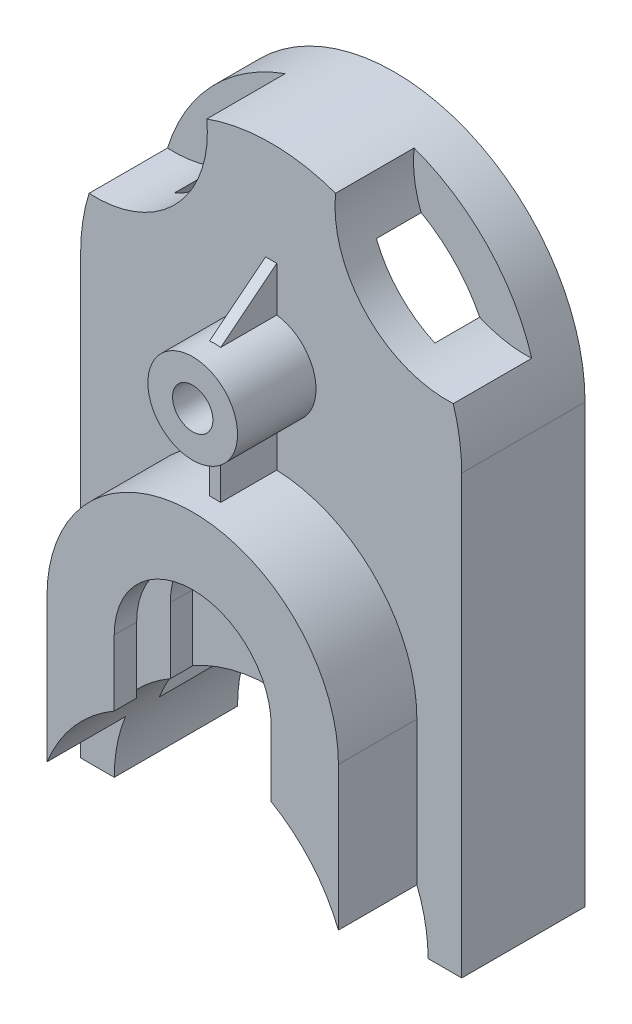
SolidWorks part; units mm, degrees
ref_plane "Front Plane" through (0, 0, 0) normal (0, 0, 1) x (1, 0, 0)
ref_plane "Top Plane" through (0, 0, 0) normal (0, 1, 0) x (1, 0, 0)
ref_plane "Right Plane" through (0, 0, 0) normal (1, 0, 0) x (0, 0, -1)
sketch "Sketch1" plane through (0, 0, 0) normal (0, 0, 1) x (1, 0, 0)
  line L1 (0, 0) -> (170, 0)
  line L2 (0, 0) -> (0, 280)
  line L3 (0, 280) -> (170, 280)
  line L4 (170, 0) -> (170, 280)
  dimension "D1" = 170
  dimension "D2" = 280
extrude "Boss-Extrude1" add sketch "Sketch1" along normal blind 90
sketch "Sketch2" plane through (0, 0, 90) normal (0, 0, 1) x (1, 0, 0)
  line L0 (170, 0) -> (170, 280) construction
  line L1 (0, 195) -> (0, 280)
  line L2 (0, 280) -> (170, 280)
  line L3 (170, 280) -> (170, 195)
  arc A0 (170, 195) -> (0, 195) centre (85, 195) ccw
  line M1 (0, 280) -> (0, 0)
  line M3 (170, 0) -> (170, 280)
  line M4 (170, 280) -> (0, 280)
  dimension "D1" = 85
  dimension "D2" = 85
  dimension "D3" = 85
  dimension "D4" = 85
  dimension "D5" = 195
  dimension "D6" = 170
  dimension "D7" = 85
  dimension "D8" = 280
  dimension "D9" = 170
  dimension "D10" = 85
extrude "Cut-Extrude1" cut sketch "Sketch2" against normal blind 90 contours A0 L2 M1 | A0 M3 M4
sketch "Sketch3" plane through (0, 0, 90) normal (0, 0, 1) x (1, 0, 0)
  line L0 (0, 0) -> (170, 0) construction
  line L1 (15, 0) -> (155, 0)
  arc A0 (155, 0) -> (15, 0) centre (85, 0) ccw
  dimension "D1" = 15
  dimension "D2" = 15
extrude "Cut-Extrude2" cut sketch "Sketch3" against normal blind 90
sketch "Sketch4" plane through (0, 0, 0) normal (0, 1, 0) x (1, 0, 0)
  line L1 (0, -90) -> (20, -90)
  line L2 (0, -90) -> (0, -55)
  line L3 (0, -55) -> (20, -55)
  line L4 (20, -90) -> (20, -55)
  line L5 (170, -90) -> (150, -90)
  line L6 (170, -90) -> (170, -55)
  line L7 (170, -55) -> (150, -55)
  line L8 (150, -90) -> (150, -55)
  dimension "D1" = 20
  dimension "D2" = 20
  dimension "D3" = 35
  dimension "D4" = 35
extrude "Cut-Extrude3" cut sketch "Sketch4" along normal blind 299
sketch "Sketch5" plane through (0, 0, 0) normal (0, 0, -1) x (-1, 0, 0)
  line L0 (-20, 195) -> (-20, 25.9808)
  line L1 (-150, 195) -> (-150, 25.9808)
  arc A0 (-20, 195) -> (-150, 195) centre (-85, 195) ccw
  arc A1 (-15, 0) -> (-155, 0) centre (-85, 0) ccw construction
  arc A2 (-20, 25.9808) -> (-150, 25.9808) centre (-85, 0) ccw
  arc M2 (-155, 0) -> (-15, 0) centre (-85, 0) cw
  dimension "D3" = 65
  dimension "D1" = 20
  dimension "D2" = 20
extrude "Cut-Extrude4" cut sketch "Sketch5" against normal blind 40 contours L0 A0 L1 M2
sketch "Sketch6" plane through (0, 0, 90) normal (0, 0, 1) x (1, 0, 0)
  circle A0 centre (85, 90) radius 9
  arc A1 (150, 249.7723) -> (20, 249.7723) centre (85, 195) ccw construction
  dimension "D1" = 18
  dimension "D2" = 85
  dimension "D3" = 90
extrude "Cut-Extrude5" cut sketch "Sketch6" against normal blind 50
sketch "Sketch7" plane through (0, 0, 90) normal (0, 0, 1) x (1, 0, 0)
  line L0 (150, 249.7723) -> (150, 25.9808) construction
  line L1 (20, 90) -> (20, 249.7723)
  line L2 (150, 90) -> (150, 249.7723)
  arc A0 (150, 90) -> (20, 90) centre (85, 90) ccw
  arc A1 (150, 249.7723) -> (20, 249.7723) centre (85, 195) ccw
  dimension "D1" = 90
  dimension "D2" = 90
  dimension "D3" = 130
  dimension "D4" = 249.7723
extrude "Cut-Extrude6" cut sketch "Sketch7" against normal blind 35
sketch "Sketch8" plane through (0, 0, 90) normal (0, 0, 1) x (1, 0, 0)
  line L0 (50, 90) -> (50, 60.6218)
  line L1 (120, 90) -> (120, 60.6218)
  arc A0 (120, 90) -> (50, 90) centre (85, 90) ccw
  arc A3 (150, 25.9808) -> (20, 25.9808) centre (85, 0) ccw construction
  arc A4 (50, 60.6218) -> (120, 60.6218) centre (85, 0) cw
  circle M1 centre (85, 90) radius 9
  arc M5 (20, 25.9808) -> (150, 25.9808) centre (85, 0) cw
  dimension "D1" = 35
  dimension "D2" = 90
  dimension "D3" = 90
extrude "Cut-Extrude7" cut sketch "Sketch8" against normal blind 35 contours L1 A0 L0 M5 M1
ref_plane "Plane1" through (0, 0, 80) normal (0, 0, 1) x (1, 0, 0)
sketch "Sketch9" plane through (0, 0, 80) normal (0, 0, 1) x (1, 0, 0)
  line L0 (35, 90) -> (50, 90)
  line L1 (120, 90) -> (135, 90)
  line L2 (35, 90) -> (35, 48.9898)
  line L3 (135, 90) -> (135, 48.9898)
  arc A0 (135, 90) -> (35, 90) centre (85, 90) ccw
  arc A1 (50, 90) -> (120, 90) centre (85, 90) cw
  arc A2 (15, 0) -> (155, 0) centre (85, 0) cw
  dimension "D1" = 50
  dimension "D2" = 90
  dimension "D3" = 90
  dimension "D4" = 15
  dimension "D5" = 15
extrude "Cut-Extrude9" cut sketch "Sketch9" against normal blind 15 contours L0 A1 L1 A0 | L2 A2 L3 L1 A1 L0
sketch "Sketch10" plane through (0, 0, 55) normal (0, 0, 1) x (1, 0, 0)
  circle A0 centre (85, 195) radius 20
  dimension "D1" = 40
extrude "Boss-Extrude2" add sketch "Sketch10" along normal blind 35
sketch "Sketch11" plane through (0, 0, 90) normal (0, 0, 1) x (1, 0, 0)
  circle A0 centre (85, 195) radius 9
  dimension "D1" = 18
extrude "Cut-Extrude10" cut sketch "Sketch11" against normal blind 35
sketch "Sketch12" plane through (0, 0, 55) normal (0, 0, 1) x (1, 0, 0)
  line L0 (0, 195) -> (0, 0) construction
  line L1 (82.5, 214.8431) -> (87.5, 214.8431)
  line L2 (82.5, 214.8431) -> (82.5, 234.8431)
  line L3 (82.5, 234.8431) -> (87.5, 234.8431)
  line L4 (87.5, 214.8431) -> (87.5, 234.8431)
  line L5 (82.5, 175.1569) -> (87.5, 175.1569)
  line L6 (82.5, 175.1569) -> (82.5, 154.9519)
  line L7 (82.5, 154.9519) -> (87.5, 154.9519)
  line L8 (87.5, 175.1569) -> (87.5, 154.9519)
  line L9 (170, 0) -> (170, 195) construction
  circle A0 centre (85, 195) radius 20 construction
  arc A1 (150, 90) -> (20, 90) centre (85, 90) ccw construction
  dimension "D1" = 5
  dimension "D2" = 5
  dimension "D3" = 82.5
  dimension "D4" = 82.5
  dimension "D5" = 82.5
  dimension "D6" = 20
extrude "Boss-Extrude3" add sketch "Sketch12" along normal blind 25
sketch "Sketch13" plane through (0, 0, 55) normal (0, 0, 1) x (1, 0, 0)
  line L0 (0, 195) -> (0, 0) construction
  arc A0 (113.7228, 275) -> (166.2404, 220) centre (163.4644, 269.9229) ccw
  arc A1 (170, 195) -> (0, 195) centre (85, 195) ccw construction
  arc A2 (56.2772, 275) -> (3.7596, 220) centre (6.5356, 269.9229) cw
  arc A3 (170, 195) -> (0, 195) centre (85, 195) ccw
  arc A4 (56.2772, 275) -> (3.7596, 220) centre (6.5356, 269.9229) cw
  arc A5 (113.7228, 275) -> (166.2404, 220) centre (163.4644, 269.9229) ccw
  point P9 (85, 280)
  point P12 (85, 280)
  dimension "D4" = 5
  dimension "D5" = 50
  dimension "D6" = 50
  dimension "D1" = 25
  dimension "D2" = 5
  dimension "D3" = 25
extrude "Cut-Extrude11" cut sketch "Sketch13" against normal blind 35
sketch "Sketch14" plane through (87.5, 0, 0) normal (1, 0, 0) x (0, 0, -1)
  line L0 (-80, 214.8431) -> (-55, 234.8431)
  line L1 (-55, 234.8431) -> (-80, 234.8431)
  line L2 (-80, 234.8431) -> (-80, 214.8431)
extrude "Cut-Extrude12" cut sketch "Sketch14" against normal blind 10
